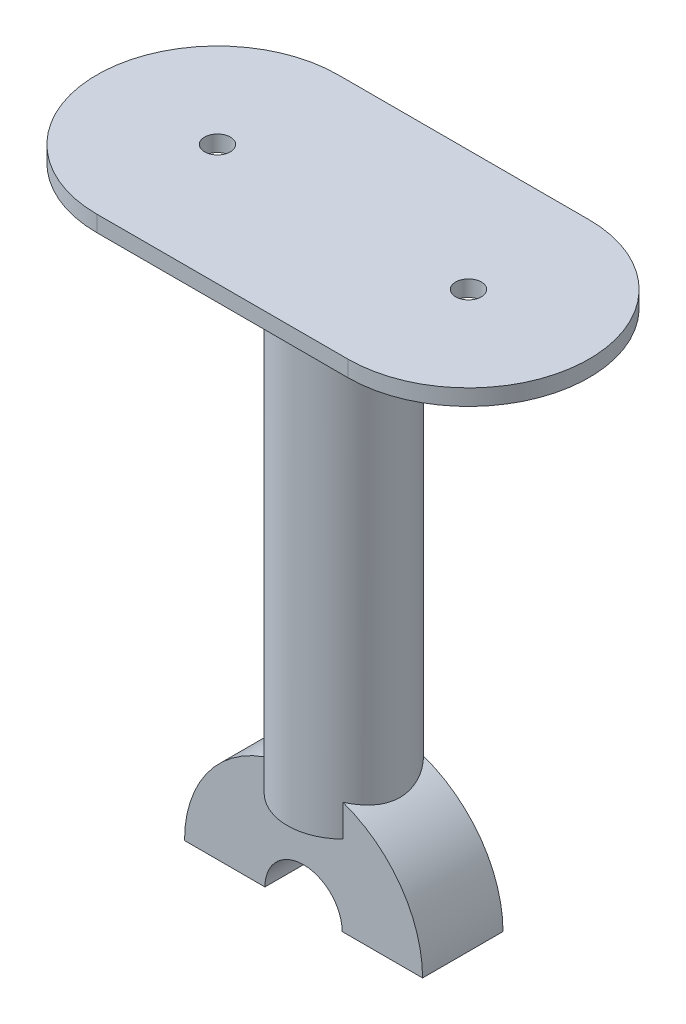
SolidWorks part; units mm, degrees
ref_plane "Front Plane" through (0, 0, 0) normal (0, 0, 1) x (1, 0, 0)
ref_plane "Top Plane" through (0, 0, 0) normal (0, 1, 0) x (1, 0, 0)
ref_plane "Right Plane" through (0, 0, 0) normal (1, 0, 0) x (0, 0, -1)
sketch "Sketch1" plane through (0, 0, 0) normal (0, 1, 0) x (1, 0, 0)
  line L0 (-4.8, 10) -> (-14.8, 10)
  line L4 (-14.8, 0) -> (-14.8, 10)
  line L8 (-4.8, 10) -> (-4.8, 0)
  line L9 (-4.8, 0) -> (-14.8, 0)
  line L10 (0, 0) -> (-4.8, 0) construction
  line L11 (0, -3.3975) -> (0, 7.4847) construction
  dimension "D1" = 10
  dimension "D2" = 10
  dimension "D3" = 4.8
revolve "Revolve1" add sketch "Sketch1" angle 180 about L11
sketch "Sketch3" plane through (0, 0, 0) normal (0, 1, 0) x (1, 0, 0)
  line L0 (0, 0) -> (0, 10) construction
  line L1 (-14.8, 0) -> (14.8, 0) construction
  line L2 (14.8, 10) -> (-14.8, 10) construction
  circle A0 centre (0, 5) radius 0.0943
  circle A1 centre (0, 5) radius 7
  dimension "D1" = 14
extrude "Boss-Extrude1" add sketch "Sketch3" along normal blind 60 from offset 10
sketch "Sketch5" plane through (0, 0, 0) normal (0, -1, 0) x (1, 0, 0)
  line L0 (14.8, -10) -> (4.8, 0) construction
  line L1 (0, 0) -> (0, -10) construction
  line L2 (4.899, -10) -> (-4.899, -10) construction
  circle A0 centre (9.8, -5) radius 2.1
  circle A1 centre (-9.8, -5) radius 2.1
  circle A2 centre (-9.8, -5) radius 2.1
  circle A3 centre (-9.8, -5) radius 2.1
extrude "Cut-Extrude1" cut sketch "Sketch5" against normal blind 6 contours A0
sketch "Sketch6" plane through (0, 0, 0) normal (0, -1, 0) x (1, 0, 0)
  line L0 (-9.8, 0) -> (-9.8, -10) construction
  line L1 (-14.8, 0) -> (-4.8, 0) construction
  line L2 (-4.8, -10) -> (-14.8, -10) construction
  circle A0 centre (-9.8, -5) radius 2.1
extrude "Cut-Extrude2" cut sketch "Sketch6" against normal blind 6 contours A0
sketch "Sketch11" plane through (0, 70, 0) normal (0, 1, 0) x (1, 0, 0)
  line L0 (-15.6999, 5) -> (15.5114, 5) construction
  line L1 (-15.6999, 20) -> (15.5114, 20)
  line L2 (-15.6999, -10) -> (15.5114, -10)
  circle A0 centre (0, 5) radius 0.0943 construction
  arc A1 (-15.6999, 20) -> (-15.6999, -10) centre (-15.6999, 5) ccw
  arc A2 (15.5114, -10) -> (15.5114, 20) centre (15.5114, 5) ccw
  circle A3 centre (15.5114, 5) radius 1.6
  circle A4 centre (-15.6999, 5) radius 1.6
  point P5 (-0.0943, 5)
  point P14 (0, 0)
  point P15 (-15.6999, 5)
extrude "Boss-Extrude3" add sketch "Sketch11" along normal blind 2 contours L2 A2 L1 A1
sketch "Sketch14" plane through (0, 72, 0) normal (0, 1, 0) x (1, 0, 0)
  line L0 (-15.6999, -10) -> (-15.6999, 20) construction
  line L1 (15.5114, 20) -> (15.5114, -10) construction
  circle A0 centre (-15.6999, 5) radius 1.6
  circle A1 centre (15.5114, 5) radius 1.6
extrude "Cut-Extrude5" cut sketch "Sketch14" against normal blind 2
